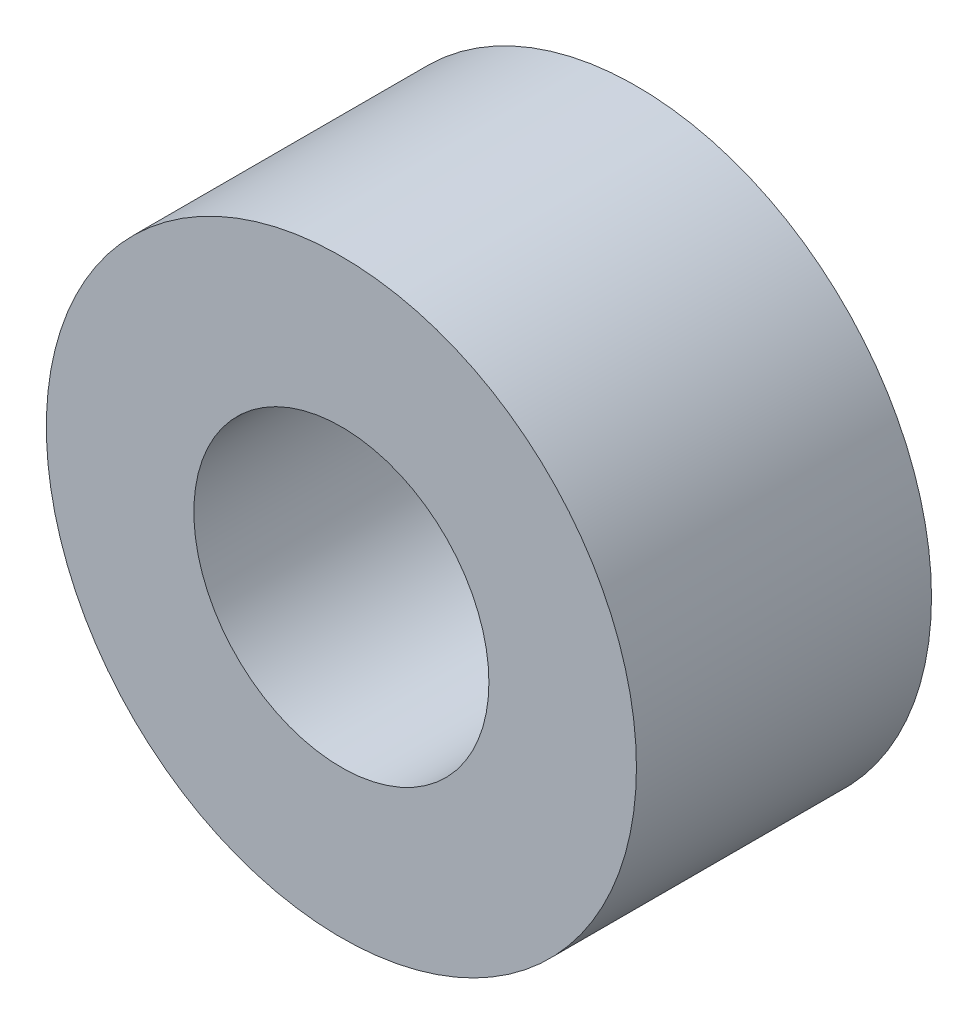
SolidWorks part; units mm, degrees
ref_plane "Front Plane" through (0, 0, 0) normal (0, 0, 1) x (1, 0, 0)
ref_plane "Top Plane" through (0, 0, 0) normal (0, 1, 0) x (1, 0, 0)
ref_plane "Right Plane" through (0, 0, 0) normal (1, 0, 0) x (0, 0, -1)
sketch "Sketch1" plane through (0, 0, 0) normal (0, 0, 1) x (1, 0, 0)
  circle A0 centre (0, 0) radius 3.175
  circle A1 centre (0, 0) radius 1.5875
  dimension "D1" = 6.35
  dimension "D2" = 3.175
extrude "Boss-Extrude1" add sketch "Sketch1" along normal blind 3.175
